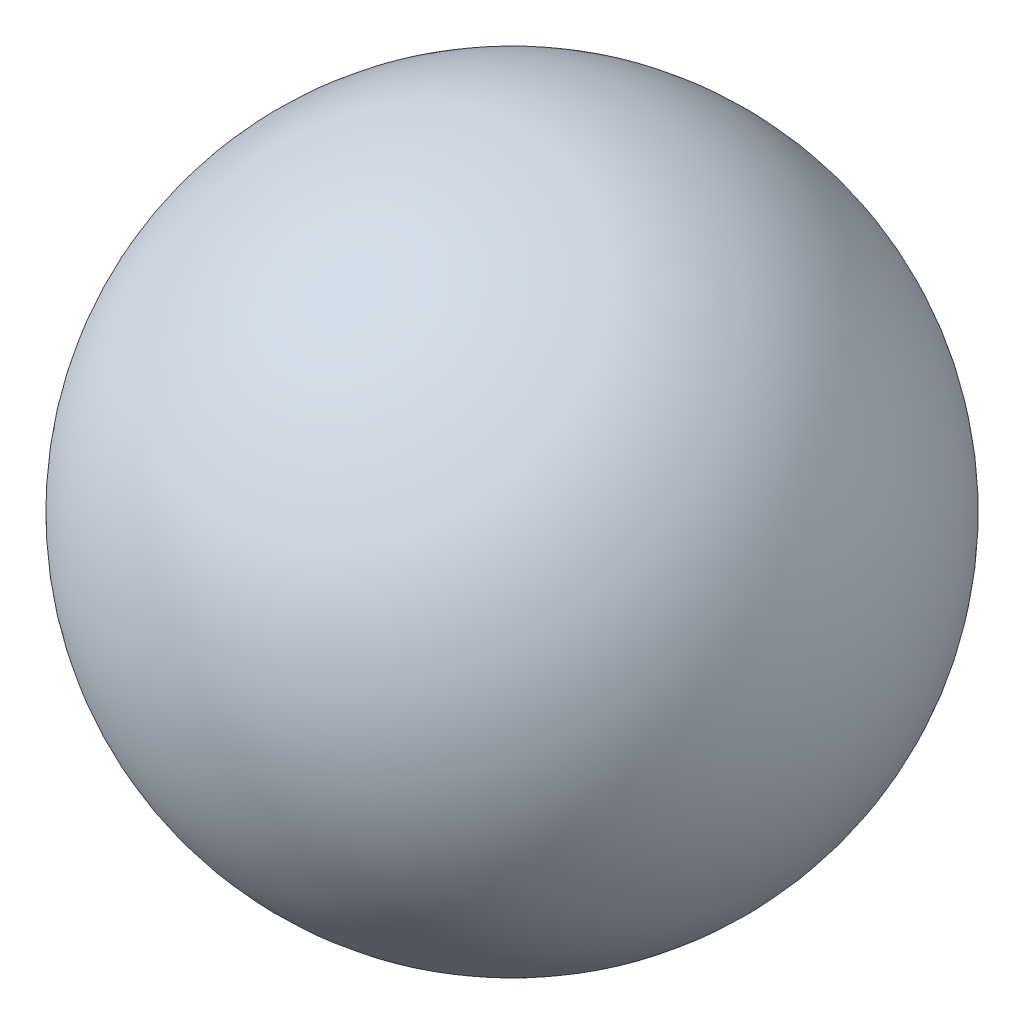
SolidWorks part; units mm, degrees
material "Rubber"
ref_plane "Front Plane" through (0, 0, 0) normal (0, 0, 1) x (1, 0, 0)
ref_plane "Top Plane" through (0, 0, 0) normal (0, 1, 0) x (1, 0, 0)
ref_plane "Right Plane" through (0, 0, 0) normal (1, 0, 0) x (0, 0, -1)
sketch "Sketch1" plane through (0, 0, 0) normal (0, 0, 1) x (1, 0, 0)
  line L1 (0, 21) -> (0, -21)
  arc A1 (0, -21) -> (0, 21) centre (0, 0) ccw
  dimension "D1" = 42
revolve "Revolve1" add sketch "Sketch1" angle 360 about L1
